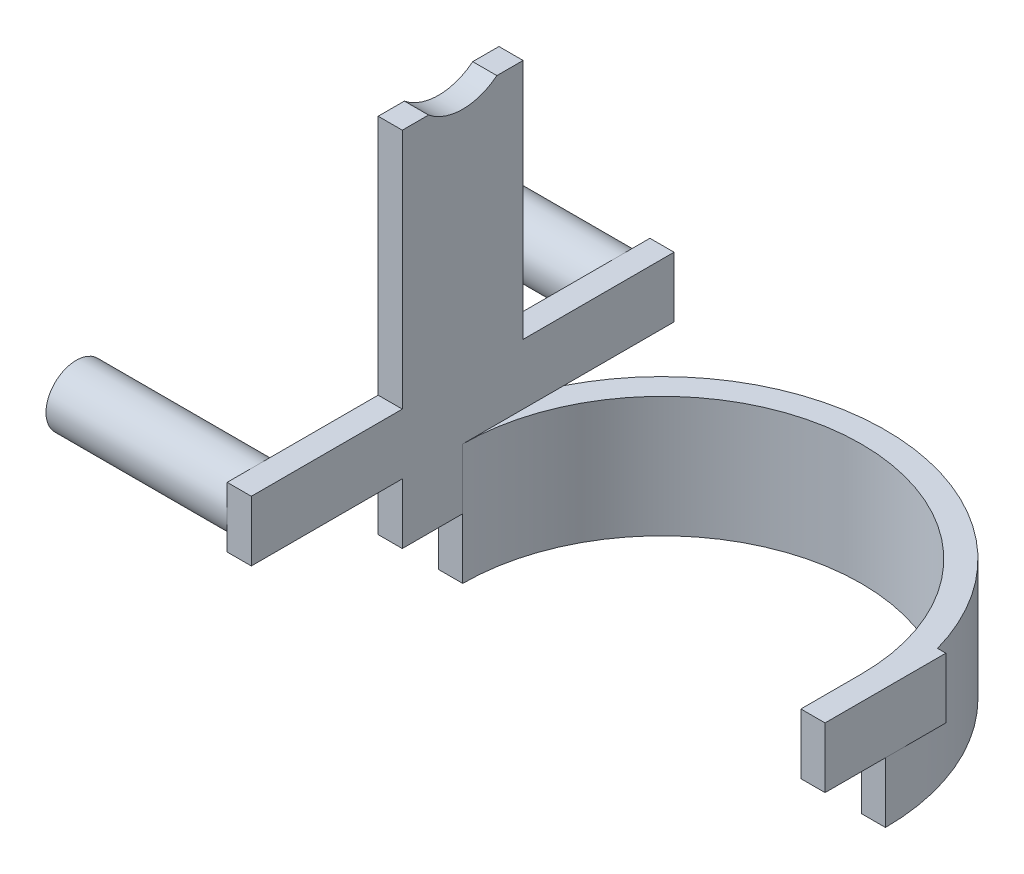
SolidWorks part; units mm, degrees
ref_plane "Front" through (0, 0, 0) normal (0, 0, 1) x (1, 0, 0)
ref_plane "Top" through (0, 0, 0) normal (0, 1, 0) x (1, 0, 0)
ref_plane "Right" through (0, 0, 0) normal (1, 0, 0) x (0, 0, -1)
sketch "草图1" plane through (0, 0, 0) normal (0, 1, 0) x (1, 0, 0)
  line L0 (-72.3418, 0) -> (74, 0) construction
  line L1 (0, 74) -> (0, -74) construction
  line L3 (-74, 20) -> (-71.2461, 20)
  line L4 (-74, 20) -> (-74, -20)
  line L5 (-74, -20) -> (-66, -20)
  line L6 (-66, 0) -> (-66, -20)
  line L7 (74, 20) -> (71.2461, 20)
  line L8 (74, 20) -> (74, -20)
  line L9 (74, -20) -> (66, -20)
  line L10 (66, 0) -> (66, -20)
  arc A0 (71.2461, 20) -> (-71.2461, 20) centre (0, 0) ccw
  arc A1 (66, 0) -> (-66, 0) centre (0, 0) ccw
  dimension "D1" = 40
  dimension "D2" = 20
  dimension "D3" = 8
  dimension "D4" = 8
  dimension "D6" = 40
  dimension "D7" = 20
extrude "凸台-拉伸1" add sketch "草图1" along normal blind 40
sketch "草图2" plane through (0, 40, 0) normal (0, 1, 0) x (1, 0, 0)
  line L1 (-74, -20) -> (-66, -20)
  line L2 (-74, -20) -> (-74, 20)
  line L3 (-74, 20) -> (-66, 20)
  line L4 (-66, -20) -> (-66, 20)
  line L5 (66, -20) -> (74, -20)
  line L6 (66, -20) -> (66, 20)
  line L7 (66, 20) -> (74, 20)
  line L8 (74, -20) -> (74, 20)
  dimension "D1" = 8
extrude "凸台-拉伸2" add sketch "草图2" along normal blind 100
sketch "草图3" plane through (-74, 0, 0) normal (-1, 0, 0) x (0, 0, 1)
  line L0 (-20, 140) -> (20, 140) construction
  circle A0 centre (0, 154) radius 18
  dimension "D1" = 14
extrude "切除-拉伸1" cut sketch "草图3" against normal through all
sketch "草图5" plane through (74, 0, 0) normal (1, 0, 0) x (0, 0, -1)
  line L1 (20, 40) -> (-67.0077, 40)
  line L2 (20, 40) -> (20, 155.015)
  line L3 (20, 155.015) -> (-67.0077, 155.015)
  line L4 (-67.0077, 40) -> (-67.0077, 155.015)
extrude "切除-拉伸2" cut sketch "草图5" against normal blind 10
sketch "草图6" plane through (0, 0, 0) normal (0, -1, 0) x (1, 0, 0)
  line L1 (-71.2461, 20) -> (-66, 20)
  line L3 (-74, 0) -> (-66, 0)
  line L4 (-66, 20) -> (-66, 0)
  line L5 (71.2461, 20) -> (66, 20)
  line L7 (74, 0) -> (66, 0)
  line L8 (66, 20) -> (66, 0)
  arc A0 (-74, 0) -> (74, 0) centre (0, 0) ccw
  circle A1 centre (0, 0) radius 85.0634
  arc A2 (71.2461, 20) -> (-71.2461, 20) centre (0, 0) ccw
extrude "切除-拉伸3" cut sketch "草图6" against normal blind 20
sketch "草图7" plane through (-74, 0, 0) normal (-1, 0, 0) x (0, 0, 1)
  line L0 (0, 0) -> (0, 85.622) construction
  line L1 (-70, 60) -> (70, 60)
  line L2 (-70, 60) -> (-70, 40)
  line L3 (-70, 40) -> (70, 40)
  line L4 (70, 60) -> (70, 40)
  dimension "D1" = 40
  dimension "D2" = 140
  dimension "D3" = 70
  dimension "D4" = 20
extrude "凸台-拉伸3" add sketch "草图7" against normal blind 8
sketch "草图9" plane through (-74, 0, 0) normal (-1, 0, 0) x (0, 0, 1)
  circle A0 centre (-60, 50) radius 10
  circle A1 centre (60, 50) radius 10
extrude "凸台-拉伸4" add sketch "草图9" along normal blind 60
